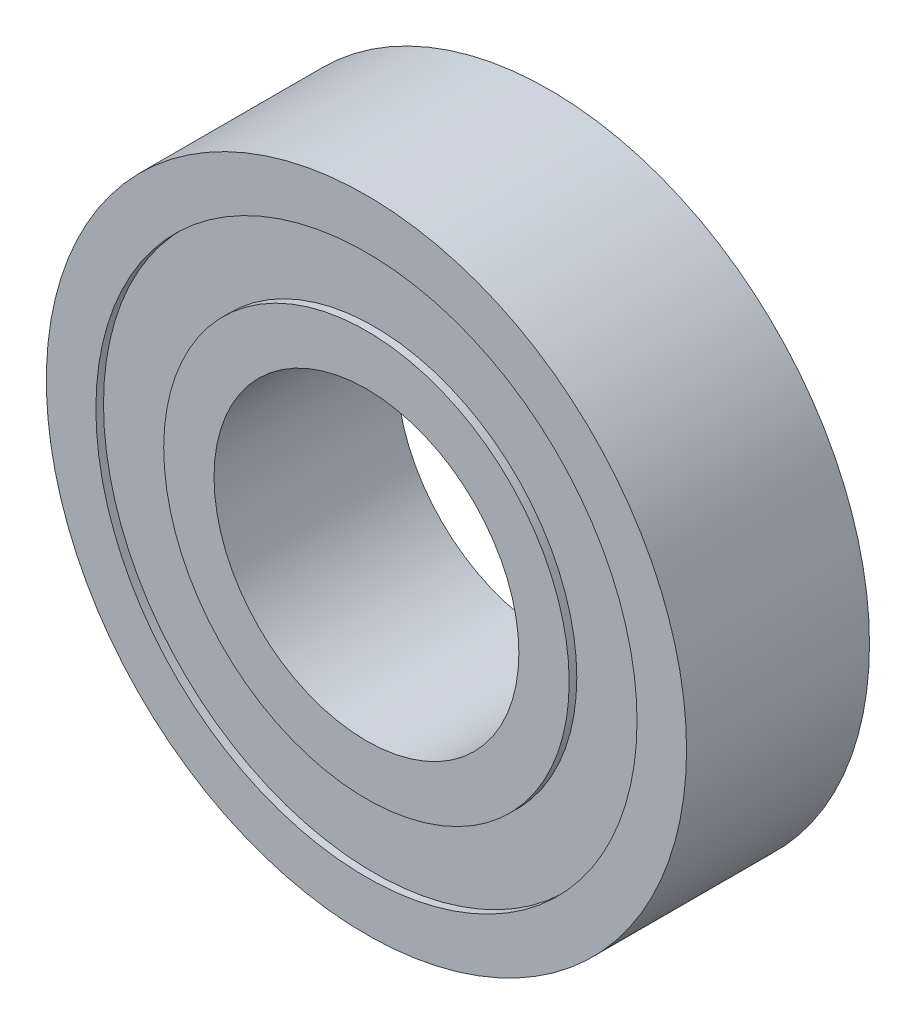
SolidWorks part; units mm, degrees
material "AISI 1035 鋼 (SS)"
ref_plane "前基準面" through (0, 0, 0) normal (0, 0, 1) x (1, 0, 0)
ref_plane "上基準面" through (0, 0, 0) normal (0, 1, 0) x (1, 0, 0)
ref_plane "右基準面" through (0, 0, 0) normal (1, 0, 0) x (0, 0, -1)
sketch "草圖1" plane through (0, 0, 0) normal (0, 0, 1) x (1, 0, 0)
  circle A0 centre (0, 0) radius 21
  dimension "D1" = 42
extrude "填料-伸長1" add sketch "草圖1" along normal mid plane 12
sketch "草圖3" plane through (0, 0, 6) normal (0, 0, 1) x (1, 0, 0)
  circle A0 centre (0, 0) radius 10
  dimension "D1" = 20
extrude "除料-伸長1" cut sketch "草圖3" against normal through all
sketch "草圖2" plane through (0, 0, 6) normal (0, 0, 1) x (1, 0, 0)
  circle A0 centre (0, 0) radius 17.75
  circle A1 centre (0, 0) radius 13.3
  dimension "D1" = 35.5
  dimension "D2" = 26.6
extrude "除料-伸長2" cut sketch "草圖2" against normal blind 0.5
mirror "鏡射1" about plane through (0, 0, 0) normal (0, 0, 1) of "除料-伸長2"
